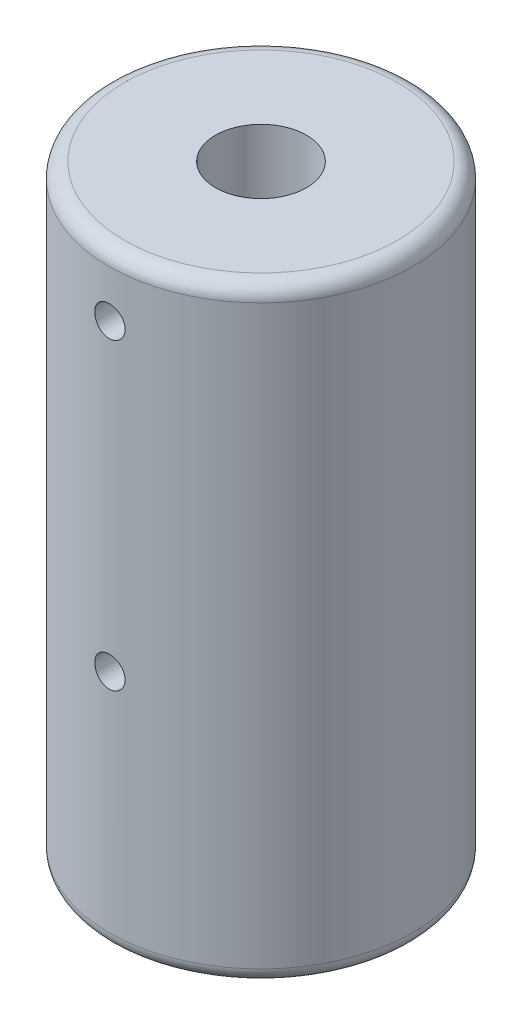
SolidWorks part; units mm, degrees
ref_plane "Front Plane" through (0, 0, 0) normal (0, 0, 1) x (1, 0, 0)
ref_plane "Top Plane" through (0, 0, 0) normal (0, 1, 0) x (1, 0, 0)
ref_plane "Right Plane" through (0, 0, 0) normal (1, 0, 0) x (0, 0, -1)
sketch "Sketch1" plane through (0, 0, 0) normal (0, 1, 0) x (1, 0, 0)
  circle A0 centre (0, 0) radius 10
extrude "Boss-Extrude1" add sketch "Sketch1" along normal blind 40
fillet "Fillet1" radius 1 1 edges at (0, 40, 10)
fillet "Fillet2" radius 1 1 edges at (0, 0, 10)
sketch "Sketch2" plane through (0, 40, 0) normal (0, 1, 0) x (1, 0, 0)
  circle A0 centre (0, 0) radius 3
extrude "Cut-Extrude1" cut sketch "Sketch2" against normal through all
sketch "Sketch3" plane through (0, 40, 0) normal (0, 1, 0) x (1, 0, 0)
  line L0 (0, 0) -> (0, -10)
  circle A0 centre (0, 0) radius 10 construction
ref_plane "Plane1" through (0, 40, 10) normal (0, 0, 1) x (1, 0, 0)
sketch "Sketch4" plane through (0, 40, 10) normal (0, 0, 1) x (1, 0, 0)
  circle A0 centre (0, -4.1066) radius 1
  circle A1 centre (0, -24.1066) radius 1
  dimension "D1" = 20
extrude "Cut-Extrude2" cut sketch "Sketch4" against normal up to next
